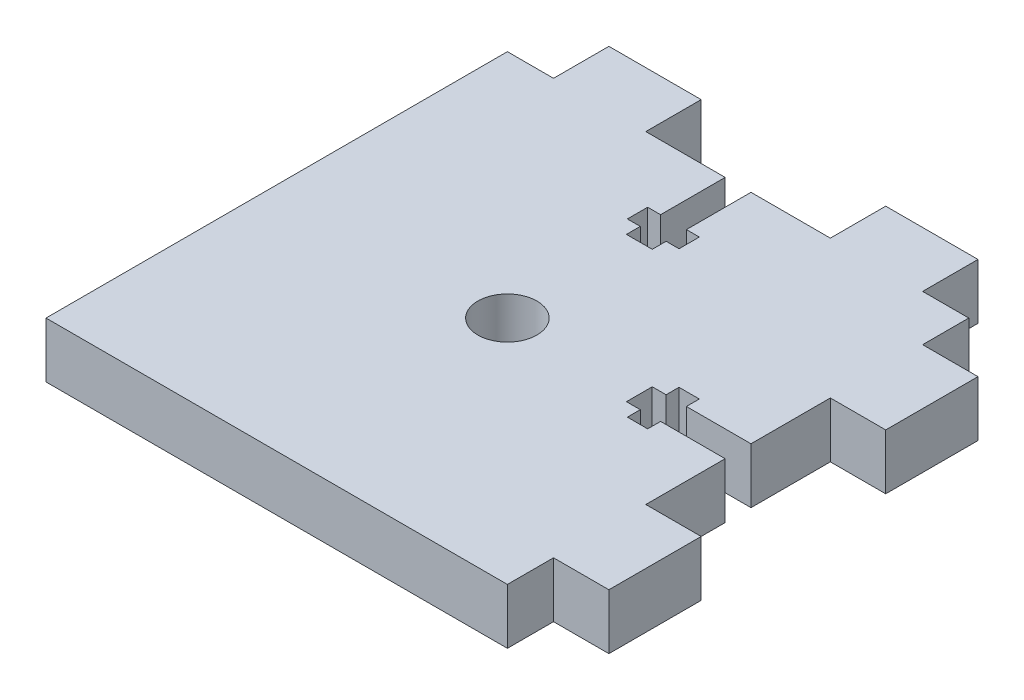
SolidWorks part; units mm, degrees
ref_plane "Спереди" through (0, 0, 0) normal (0, 0, 1) x (1, 0, 0)
ref_plane "Сверху" through (0, 0, 0) normal (0, 1, 0) x (1, 0, 0)
ref_plane "Справа" through (0, 0, 0) normal (1, 0, 0) x (0, 0, -1)
sketch "Эскиз1" plane through (0, 0, 0) normal (0, 1, 0) x (1, 0, 0)
  line L44 (-27.604, 22.0349) -> (-27.604, -27.9651)
  line L45 (22.396, -27.9651) -> (22.396, -22.9651)
  line L46 (-27.604, -27.9651) -> (22.396, -27.9651)
  line L47 (17.396, 28.0349) -> (7.396, 28.0349)
  line L48 (22.396, 22.0349) -> (17.396, 22.0349)
  line L49 (17.396, 22.0349) -> (17.396, 28.0349)
  line L50 (7.396, 28.0349) -> (7.396, 22.0346)
  line L51 (-12.604, 22.0349) -> (-12.604, 28.0349)
  line L52 (-12.604, 28.0349) -> (-22.604, 28.0349)
  line L53 (7.396, 22.0346) -> (-1.204, 22.0348)
  line L54 (-22.604, 28.0349) -> (-22.604, 22.0349)
  line L55 (-22.604, 22.0349) -> (-27.604, 22.0349)
  line L56 (28.396, -12.9651) -> (22.396, -12.9651)
  line L57 (22.396, -22.9651) -> (28.396, -22.9651)
  line L58 (28.396, -22.9651) -> (28.396, -12.9651)
  line L59 (22.396, 17.0349) -> (22.396, 22.0349)
  line L60 (28.3956, 17.0349) -> (22.396, 17.0349)
  line L61 (22.3956, 7.0349) -> (28.3956, 7.0349)
  line L62 (22.396, -12.9651) -> (22.396, -4.3651)
  line L63 (28.3956, 7.0349) -> (28.3956, 17.0349)
  line L64 (13.1956, -1.5653) -> (11.6956, -1.5664)
  line L65 (15.3956, -1.5651) -> (15.3953, -0.165)
  line L66 (15.3953, -0.165) -> (13.1945, -0.1654)
  line L67 (13.1945, -0.1654) -> (13.1956, -1.5653)
  line L68 (15.3987, -5.765) -> (15.3985, -4.3651)
  line L69 (13.1987, -5.7653) -> (15.3987, -5.765)
  line L70 (11.6977, -4.3655) -> (13.1977, -4.3644)
  line L71 (22.3956, -1.5651) -> (15.3956, -1.5651)
  line L72 (13.1977, -4.3644) -> (13.1987, -5.7653)
  line L73 (11.6956, -1.5664) -> (11.6977, -4.3655)
  line L74 (15.3985, -4.3651) -> (22.396, -4.3651)
  line L75 (22.3956, -1.5651) -> (22.3956, 7.0349)
  line L76 (-4.0042, 12.8348) -> (-4.0033, 11.3348)
  line L77 (-4.004, 15.0348) -> (-5.4041, 15.0348)
  line L78 (-5.4041, 15.0348) -> (-5.4041, 12.834)
  line L79 (-5.4041, 12.834) -> (-4.0042, 12.8348)
  line L80 (0.1948, 15.0375) -> (-1.204, 15.0373)
  line L81 (0.1948, 12.8373) -> (0.1948, 15.0375)
  line L82 (-1.2052, 11.3365) -> (-1.2061, 12.8365)
  line L83 (-4.004, 22.0348) -> (-4.004, 15.0348)
  line L84 (-1.2061, 12.8365) -> (0.1948, 12.8373)
  line L85 (-4.0033, 11.3348) -> (-1.2052, 11.3365)
  line L86 (-1.204, 15.0373) -> (-1.204, 22.0348)
  line L87 (-4.004, 22.0348) -> (-12.604, 22.0349)
  line L88 (-27.604, 22.0349) -> (31.1951, 22.0349) construction
  line L89 (22.396, 28.0349) -> (22.396, -29.8583) construction
  circle A1 centre (-2.604, -2.9651) radius 3.2
  point P49 (18.8956, -1.5651)
  point P50 (18.8973, -4.3651)
  dimension "D6" = 6.4
  dimension "D1" = 6
  dimension "D2" = 10
  dimension "D3" = 6
  dimension "D4" = 10
  dimension "D5" = 50
  dimension "D7" = 6
  dimension "D8" = 6
  dimension "D9" = 10
  dimension "D10" = 10
  dimension "D11" = 50
  dimension "D12" = 25
  dimension "D13" = 25
  dimension "D14" = 2.8
  dimension "D15" = 5
  dimension "D16" = 5
  dimension "D17" = 23.6
  dimension "D18" = 23.6
  dimension "D19" = 5
  dimension "D20" = 5
  dimension "D21" = 23.6
  dimension "D22" = 2.8
  dimension "D23" = 23.6
extrude "Бобышка-Вытянуть1" add sketch "Эскиз1" along normal blind 6
